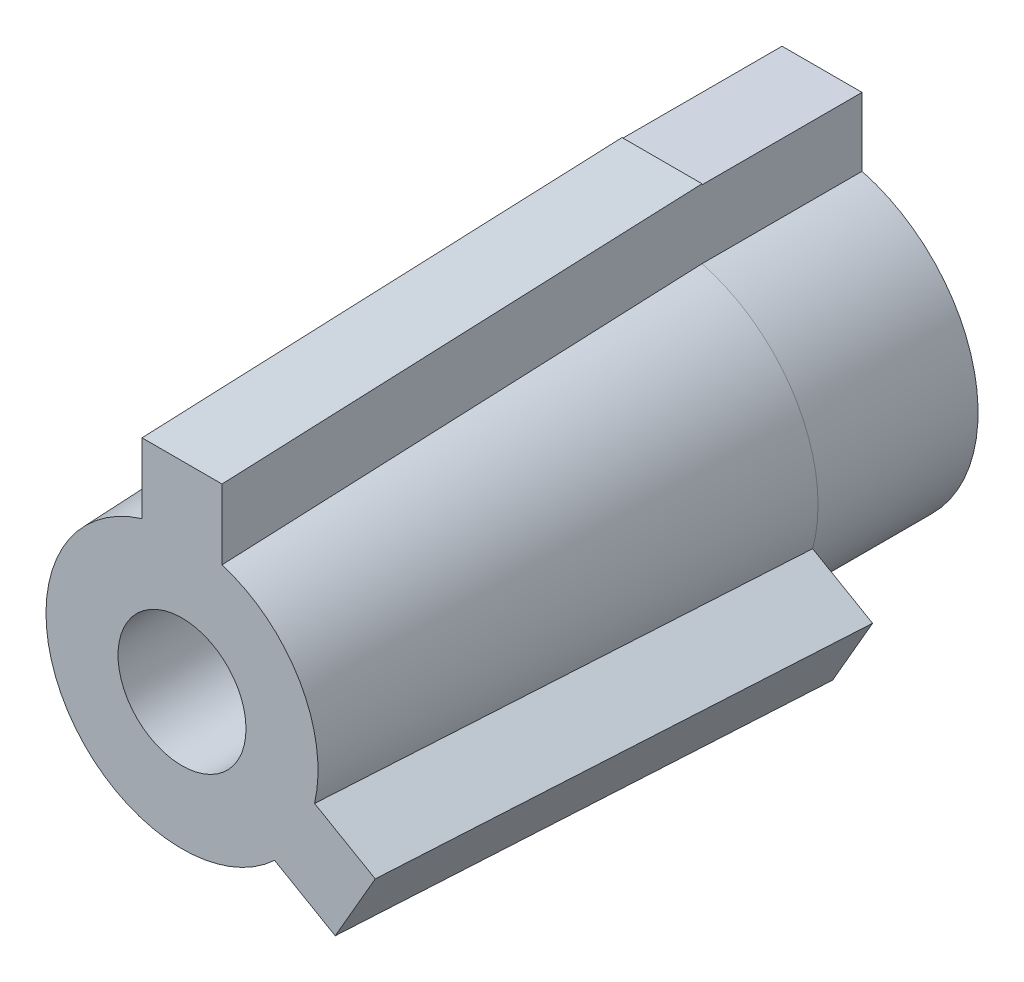
SolidWorks part; units mm, degrees
ref_plane "Front Plane" through (0, 0, 0) normal (0, 0, 1) x (1, 0, 0)
ref_plane "Top Plane" through (0, 0, 0) normal (0, 1, 0) x (1, 0, 0)
ref_plane "Right Plane" through (0, 0, 0) normal (1, 0, 0) x (0, 0, -1)
sketch "Sketch1" plane through (0, 0, 0) normal (0, 0, 1) x (1, 0, 0)
  circle A0 centre (0, 0) radius 9.75
  circle A1 centre (0, 0) radius 4
  circle A2 centre (0, 0) radius 8.5
  dimension "D1" = 19.5
  dimension "D2" = 8
  dimension "D3" = 17
extrude "Boss-Extrude1" add sketch "Sketch1" along normal blind 30 contours A2 A1
sketch "Sketch2" plane through (0, 0, 0) normal (0, 0, -1) x (-1, 0, 0)
  circle A0 centre (0, 0) radius 9.75
  circle A2 centre (0, 0) radius 8.5
  circle A3 centre (0, 0) radius 8.5
  dimension "D1" = 19.5
  dimension "D2" = 0
ref_plane "Plane1" through (0, 0, 30) normal (0, 0, 1) x (1, 0, 0)
extrude "Boss-Extrude2" add sketch "Sketch2" along normal blind 10 contours A0
loft "Loft4" add section edge at (8.5, 0, 30) section edge at (-9.75, 0, 0)
sketch "Sketch4" plane through (0, 0, 30) normal (0, 0, 1) x (1, 0, 0)
  circle A0 centre (0, 0) radius 4
  dimension "D1" = 8
extrude "Cut-Extrude1" cut sketch "Sketch4" against normal blind 40
sketch "Sketch5" plane through (0, 0, 0) normal (0, 0, 1) x (1, 0, 0)
  line L0 (0, 0) -> (0, 10.9437) construction
  line L1 (0, 9.75) -> (-6.029, 9.75) construction
  line L2 (0, 9.75) -> (4.896, 9.75) construction
  line L4 (-2.5, 13.75) -> (2.5, 13.75)
  line L5 (-2.5, 13.75) -> (-2.5, 8.615)
  line L6 (-2.5, 8.615) -> (2.5, 8.615)
  line L7 (2.5, 13.75) -> (2.5, 8.615)
  circle A0 centre (0, 0) radius 9.75 construction
  dimension "D1" = 2.5
  dimension "D2" = 5
  dimension "D3" = 4
sketch "Sketch6" plane through (0, 0, 30) normal (0, 0, 1) x (1, 0, 0)
  line L0 (0, 0) -> (0, 10.9437) construction
  line L1 (0, 8.5) -> (-6.4063, 8.5) construction
  line L2 (0, 8.5) -> (5.1997, 8.5) construction
  line L4 (-2.5, 12.5) -> (2.5, 12.5)
  line L5 (-2.5, 12.5) -> (-2.5, 6.3577)
  line L6 (-2.5, 6.3577) -> (2.5, 6.3577)
  line L7 (2.5, 12.5) -> (2.5, 6.3577)
  circle A0 centre (0, 0) radius 8.5 construction
  dimension "D1" = 2.5
  dimension "D2" = 5
  dimension "D3" = 4
loft "Loft5" add profiles "Sketch6", "Sketch5"
pattern_circular "CirPattern1" count 2 every 240 about axis through (0, 0, 0) along (0, 0, 1) of "Loft5"
sketch "Sketch7" plane through (0, 0, -10) normal (0, 0, -1) x (-1, 0, 0)
  line L0 (0, 0) -> (0, 19.389) construction
  line L1 (0, 9.6945) -> (-10.1184, 9.6945) construction
  line L2 (0, 9.6945) -> (8.9217, 9.6945) construction
  line L4 (-2.5, 13.6945) -> (2.5, 13.6945)
  line L5 (-2.5, 13.6945) -> (-2.5, 8.1444)
  line L6 (-2.5, 8.1444) -> (2.5, 8.1444)
  line L7 (2.5, 13.6945) -> (2.5, 8.1444)
  dimension "D1" = 2.5
  dimension "D2" = 2.5
  dimension "D3" = 4
extrude "Boss-Extrude3" add sketch "Sketch7" against normal blind 10
